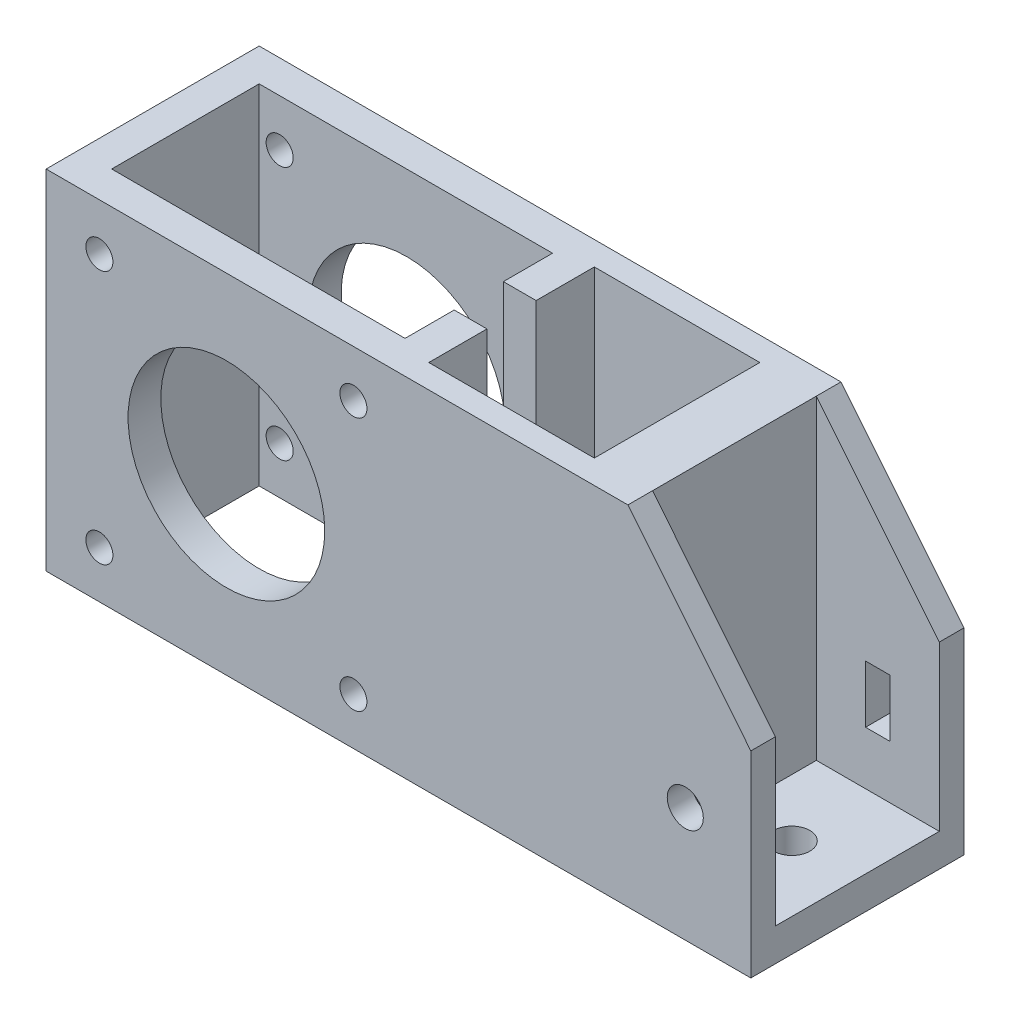
SolidWorks part; units mm, degrees
ref_plane "Plan de face" through (0, 0, 0) normal (0, 0, 1) x (1, 0, 0)
ref_plane "Plan de dessus" through (0, 0, 0) normal (0, 1, 0) x (1, 0, 0)
ref_plane "Plan de droite" through (0, 0, 0) normal (1, 0, 0) x (0, 0, -1)
sketch "Esquisse1" plane through (0, 0, 0) normal (0, 0, 1) x (1, 0, 0)
  line L0 (0, 0) -> (0, -42.5)
  line L1 (0, -42.5) -> (86, -42.5)
  line L2 (86, -42.5) -> (86, -18.5)
  line L3 (86, -18.5) -> (71, 0)
  line L4 (71, 0) -> (0, 0)
  dimension "D1" = 42.5
  dimension "D2" = 86
  dimension "D3" = 24
  dimension "D4" = 71
  dimension "D5" = 15
extrude "Boss.-Extru.1" add sketch "Esquisse1" along normal blind 26
sketch "Esquisse2" plane through (0, 0, 26) normal (0, 0, 1) x (1, 0, 0)
  line L0 (0, 0) -> (0, -42.5) construction
  line L1 (22, -21.25) -> (0, -21.25) construction
  circle A0 centre (22, -21.25) radius 12
  dimension "D1" = 22
  dimension "D2" = 24
extrude "Enlèv. mat.-Extru.1" cut sketch "Esquisse2" against normal through all
sketch "Esquisse3" plane through (0, 0, 0) normal (0, 1, 0) x (1, 0, 0)
  line L1 (4, -4) -> (39.8, -4)
  line L2 (4, -4) -> (4, -22)
  line L3 (4, -22) -> (39.8, -22)
  line L4 (39.8, -4) -> (39.8, -22)
  line L5 (43.8, -2.9) -> (64, -2.9)
  line L6 (43.8, -2.9) -> (43.8, -23.1)
  line L7 (43.8, -23.1) -> (64, -23.1)
  line L8 (64, -2.9) -> (64, -23.1)
  line L9 (0, -26) -> (0, 0) construction
  line L11 (71, -26) -> (71, 0) construction
  line L12 (64, -13) -> (71, -13) construction
  line L13 (4, -13) -> (0, -13) construction
  dimension "D2" = 4
  dimension "D4" = 4
  dimension "D5" = 7
  dimension "D6" = 20.2
  dimension "D7" = 20.2
  dimension "D8" = 18
extrude "Enlèv. mat.-Extru.2" cut sketch "Esquisse3" against normal through all
sketch "Esquisse4" plane through (0, 0, 0) normal (0, 1, 0) x (1, 0, 0)
  line L0 (71, -26) -> (71, 0) construction
  line L1 (71, -3) -> (86, -3)
  line L2 (71, -3) -> (71, -23)
  line L3 (71, -23) -> (86, -23)
  line L4 (86, -3) -> (86, -23)
  line L5 (86, -26) -> (86, 0) construction
  line L6 (86, -26) -> (71, -26) construction
  line L7 (86, 0) -> (71, 0) construction
  dimension "D1" = 3
  dimension "D2" = 3
extrude "Enlèv. mat.-Extru.3" cut sketch "Esquisse4" against normal offset from surface (38.5 mm away) 4 up to face at (53.9, -42.5, 13)
hole_wizard "Dégagement M31" positions "Esquisse6" profile "Esquisse5" hole size "M3" standard "Din" end condition through all
sketch "Esquisse6" plane through (0, 0, 26) normal (0, 0, 1) x (1, 0, 0)
  line L1 (6.5, -5.75) -> (37.5, -5.75) construction
  line L2 (6.5, -5.75) -> (6.5, -36.75) construction
  line L3 (6.5, -36.75) -> (37.5, -36.75) construction
  line L4 (37.5, -5.75) -> (37.5, -36.75) construction
  line L5 (6.5, -5.75) -> (37.5, -36.75) construction
  line L6 (6.5, -36.75) -> (37.5, -5.75) construction
  line L7 (0, 0) -> (0, -42.5) construction
  line L8 (71, 0) -> (0, 0) construction
  point P0 (22, -21.25)
  point P1 (37.5, -36.75)
  point P4 (6.5, -5.75)
  point P5 (6.5, -36.75)
  point P6 (37.5, -5.75)
  dimension "D1" = 31
  dimension "D2" = 31
  dimension "D3" = 6.5
  dimension "D4" = 5.75
sketch "Esquisse5" plane through (22, -21.25, 26) normal (1, 0, 0) x (0, -1, 0)
  line L0 (0, 0) -> (0, 26)
  line L1 (0, 26) -> (1.65, 26)
  line L2 (1.65, 26) -> (1.65, 0)
  line L5 (1.65, 0) -> (0, 0)
  line L11 (0, -6.35) -> (0, 107.95) construction
  dimension "Diamètre du perçage jusqu'au prochain" = 3.3
  dimension "Profondeur du perçage jusqu'au prochain" = 26
sketch "Esquisse7" plane through (39.8, 0, 0) normal (-1, 0, 0) x (0, 0, 1)
  line L0 (22, -42.5) -> (4, -42.5) construction
  line L1 (10, 0) -> (16, 0)
  line L2 (10, 0) -> (10, -16)
  line L3 (10, -16) -> (16, -16)
  line L4 (16, 0) -> (16, -16)
  line L5 (10, -26.5) -> (16, -26.5)
  line L6 (10, -26.5) -> (10, -42.5)
  line L7 (10, -42.5) -> (16, -42.5)
  line L8 (16, -26.5) -> (16, -42.5)
  line L9 (22, 0) -> (4, 0) construction
  line L12 (13, 0) -> (13, -42.5) construction
  line L13 (26, -42.5) -> (0, -42.5) construction
  dimension "D1" = 6
  dimension "D4" = 16
  dimension "D5" = 16
  dimension "D6" = 10.5
extrude "Enlèv. mat.-Extru.4" cut sketch "Esquisse7" against normal up to next
hole_wizard "Dégagement M41" positions "Esquisse9" profile "Esquisse8" hole size "M4" standard "Din"
sketch "Esquisse9" plane through (0, -38.5, 0) normal (0, 1, 0) x (1, 0, 0)
  line L0 (86, -3) -> (86, -23) construction
  line L1 (71, -3) -> (86, -3) construction
  point P0 (78, -13)
  point P1 (86, -13)
  dimension "D1" = 8
  dimension "D2" = 10
sketch "Esquisse8" plane through (78, -38.5, 13) normal (1, 0, 0) x (0, 0, 1)
  line L0 (0, 0) -> (0, 24)
  line L1 (0, 24) -> (2.2, 24)
  line L2 (2.2, 24) -> (2.2, 0)
  line L5 (2.2, 0) -> (0, 0)
  line L10 (0, 24) -> (-2.2, 24) construction
  line L11 (0, -6.35) -> (0, 107.95) construction
  dimension "Diamètre du perçage" = 4.4
  dimension "Profondeur du perçage" = 24
  dimension "Angle de pointe" = 180
hole_wizard "Dégagement M42" positions "Esquisse11" profile "Esquisse10" hole size "M4" standard "Din"
sketch "Esquisse11" plane through (0, 0, 23) normal (0, 0, -1) x (-1, 0, 0)
  line L0 (-86, -38.5) -> (-86, -18.5) construction
  line L1 (-86, -38.5) -> (-71, -38.5) construction
  point P0 (-78, -28.5)
  dimension "D1" = 8
  dimension "D2" = 10
sketch "Esquisse10" plane through (78, -28.5, 23) normal (1, 0, 0) x (0, 1, 0)
  line L0 (0, 0) -> (0, 24)
  line L1 (0, 24) -> (2.2, 24)
  line L2 (2.2, 24) -> (2.2, 0)
  line L5 (2.2, 0) -> (0, 0)
  line L10 (0, 24) -> (-2.2, 24) construction
  line L11 (0, -6.35) -> (0, 107.95) construction
  dimension "Diamètre du perçage" = 4.4
  dimension "Profondeur du perçage" = 24
  dimension "Angle de pointe" = 180
sketch "Esquisse12" plane through (0, 0, 3) normal (0, 0, 1) x (1, 0, 0)
  line L0 (71, -38.5) -> (86, -38.5) construction
  line L1 (77, -25) -> (80, -25)
  line L2 (77, -25) -> (77, -32)
  line L3 (77, -32) -> (80, -32)
  line L4 (80, -25) -> (80, -32)
  line L5 (86, -38.5) -> (86, -18.5) construction
  dimension "D1" = 3
  dimension "D2" = 7
  dimension "D3" = 6.5
  dimension "D4" = 6
extrude "Enlèv. mat.-Extru.5" cut sketch "Esquisse12" against normal up to next
